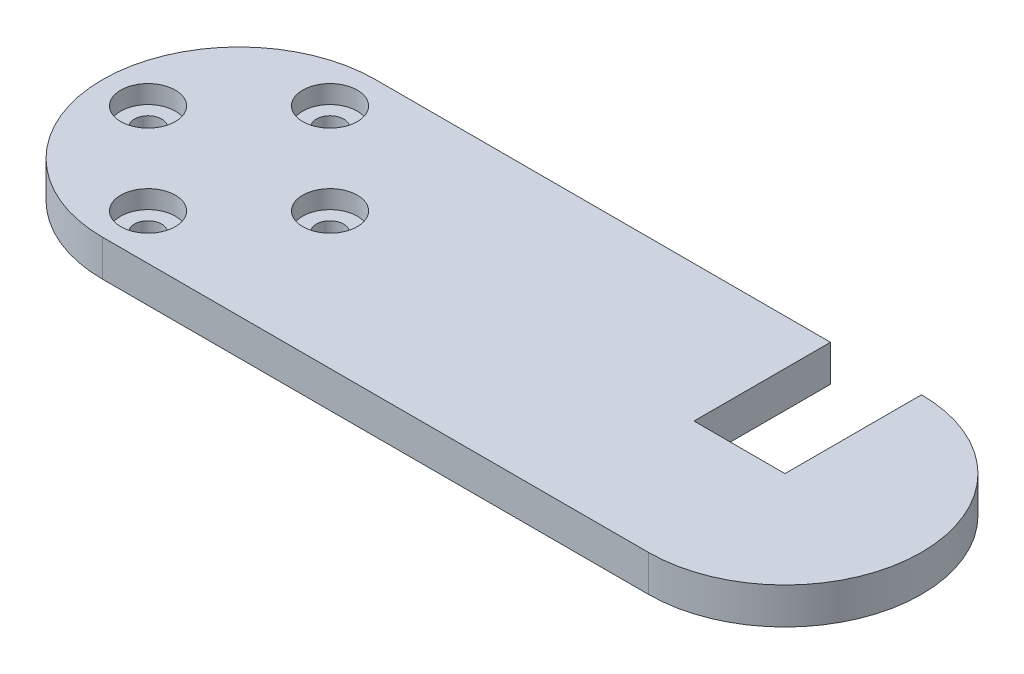
SolidWorks part; units mm, degrees
ref_plane "Front Plane" through (0, 0, 0) normal (0, 0, 1) x (1, 0, 0)
ref_plane "Top Plane" through (0, 0, 0) normal (0, 1, 0) x (1, 0, 0)
ref_plane "Right Plane" through (0, 0, 0) normal (1, 0, 0) x (0, 0, -1)
sketch "Sketch1" plane through (0, 0, 0) normal (0, 1, 0) x (1, 0, 0)
  line L0 (0, 0) -> (60, 0) construction
  line L1 (0, 15) -> (60, 15)
  line L2 (0, -15) -> (60, -15)
  arc A0 (0, 15) -> (0, -15) centre (0, 0) ccw
  arc A1 (60, -15) -> (60, 15) centre (60, 0) ccw
  point P3 (30, 0)
  dimension "D2" = 15
  dimension "D1" = 60
extrude "Boss-Extrude1" add sketch "Sketch1" along normal blind 4
sketch "Sketch2" plane through (0, 4, 0) normal (0, 1, 0) x (1, 0, 0)
  line L0 (60, 15) -> (0, 15) construction
  line L2 (70, -15) -> (70, -11.1803)
  line L3 (60, 15) -> (50, 15)
  line L4 (50, 0) -> (50, 15)
  line L5 (70, -15) -> (68.3205, -12.4808) construction
  line L6 (70, 15) -> (68.3205, 12.4808) construction
  line L7 (70, 11.1803) -> (70, 15)
  line L8 (60, 15) -> (60, 0)
  line L9 (50, 0) -> (60, 0)
  arc A0 (70, 11.1803) -> (68.3205, 12.4808) centre (60, 0) ccw
  arc A1 (68.3205, -12.4808) -> (70, -11.1803) centre (60, 0) ccw
  line M8 (60, 15) -> (0, 15)
  dimension "D1" = 20
extrude "Cut-Extrude1" cut sketch "Sketch2" against normal blind 4 contours L4 L9 L8 M8
sketch "Sketch3" plane through (0, 4, 0) normal (0, 1, 0) x (1, 0, 0)
  circle A0 centre (0, 0) radius 10 construction
  circle A1 centre (-10, 0) radius 3
  circle A2 centre (0, 10) radius 3
  circle A3 centre (10, 0) radius 3
  circle A4 centre (0, -10) radius 3
  point P14 (0, 0)
  dimension "D1" = 20
  dimension "D2" = 6
  dimension "D3" = 4
extrude "Cut-Extrude2" cut sketch "Sketch3" against normal blind 2
sketch "Sketch4" plane through (0, 2, 0) normal (0, 1, 0) x (1, 0, 0)
  circle A0 centre (-10, 0) radius 1.5
  circle A1 centre (0, 10) radius 1.5
  circle A2 centre (10, 0) radius 1.5
  circle A3 centre (0, -10) radius 1.5
  point P12 (0, 0)
  dimension "D1" = 3
  dimension "D2" = 4
extrude "Cut-Extrude3" cut sketch "Sketch4" against normal blind 2
